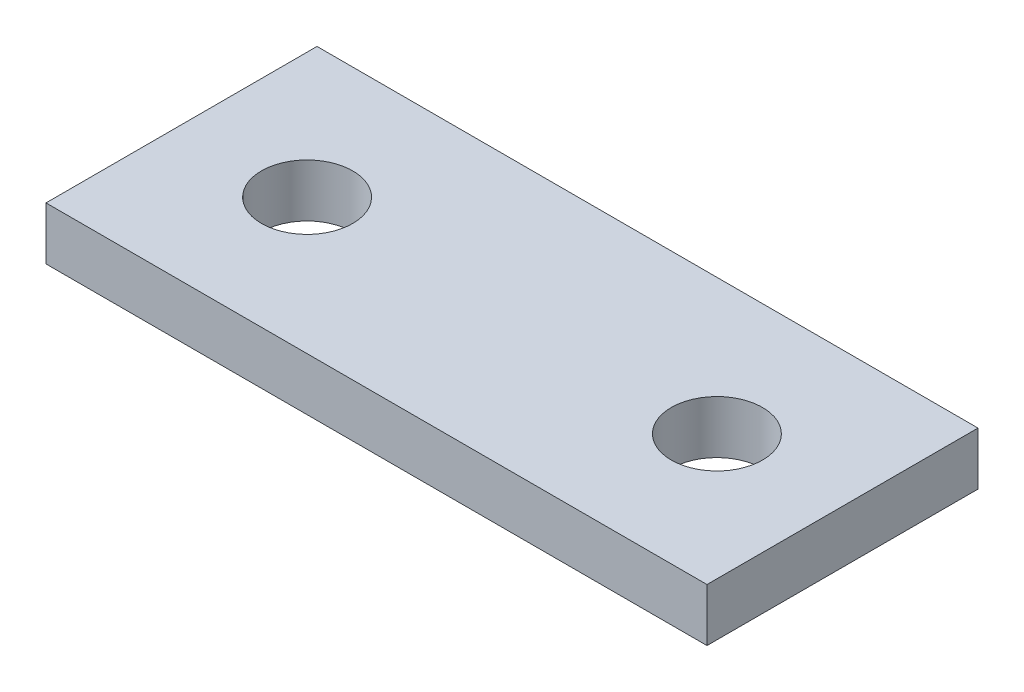
SolidWorks part; units mm, degrees
ref_plane "Front Plane" through (0, 0, 0) normal (0, 0, 1) x (1, 0, 0)
ref_plane "Top Plane" through (0, 0, 0) normal (0, 1, 0) x (1, 0, 0)
ref_plane "Right Plane" through (0, 0, 0) normal (1, 0, 0) x (0, 0, -1)
sketch "Sketch1" plane through (0, 0, 0) normal (0, 1, 0) x (1, 0, 0)
  line L1 (-11.6504, 2.529) -> (13.7496, 2.529)
  line L2 (-11.6504, 2.529) -> (-11.6504, -7.885)
  line L3 (-11.6504, -7.885) -> (13.7496, -7.885)
  line L4 (13.7496, 2.529) -> (13.7496, -7.885)
  circle A0 centre (-6.8244, -2.678) radius 1.7526
  circle A1 centre (8.9236, -2.678) radius 1.7526
  dimension "D3" = 3.5052
  dimension "D4" = 3.5052
  dimension "D1" = 25.4
  dimension "D2" = 10.414
  dimension "D5" = 4.826
  dimension "D6" = 4.826
extrude "Boss-Extrude1" add sketch "Sketch1" along normal blind 2.032
equation "\"0..8in\"=0.1"
